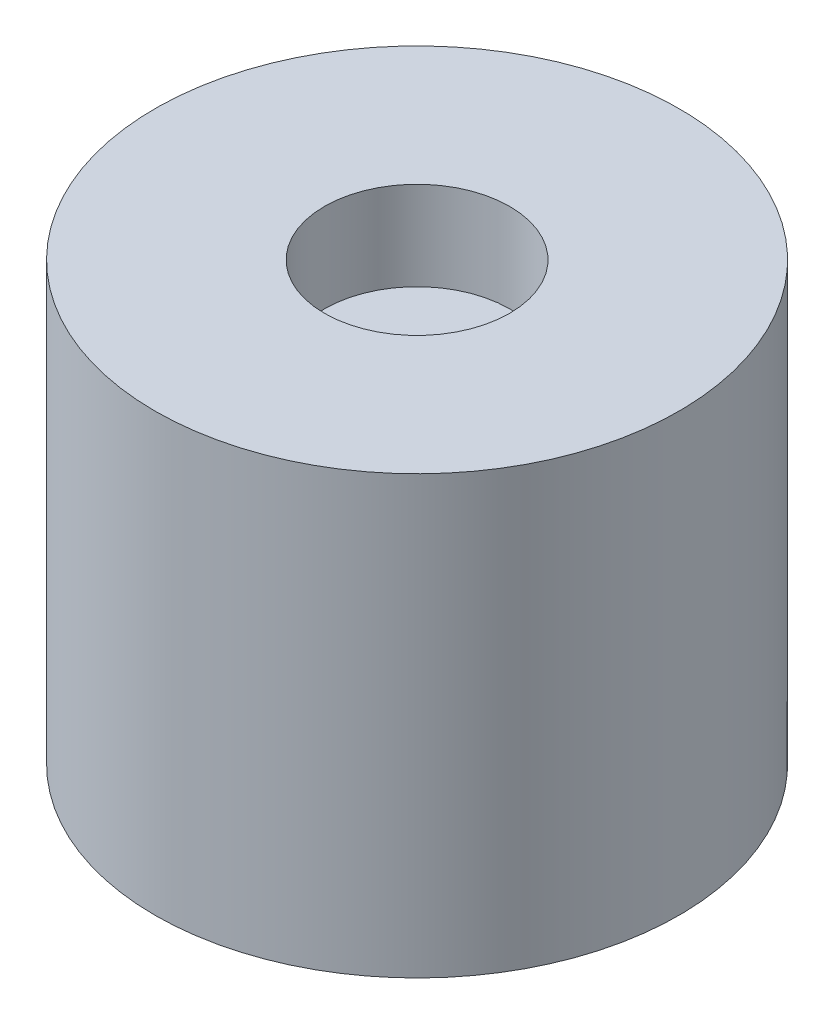
SolidWorks part; units mm, degrees
ref_plane "Front Plane" through (0, 0, 0) normal (0, 0, 1) x (1, 0, 0)
ref_plane "Top Plane" through (0, 0, 0) normal (0, 1, 0) x (1, 0, 0)
ref_plane "Right Plane" through (0, 0, 0) normal (1, 0, 0) x (0, 0, -1)
sketch "Sketch1" plane through (0, 0, 0) normal (0, 1, 0) x (1, 0, 0)
  circle A0 centre (0, 0) radius 6
  dimension "D1" = 12
extrude "Boss-Extrude1" add sketch "Sketch1" along normal blind 10
sketch "Sketch3" plane through (0, 10, 0) normal (0, 1, 0) x (1, 0, 0)
  circle A0 centre (0, 0) radius 2.1209
  dimension "D1" = 4.2418
extrude "Cut-Extrude2" cut sketch "Sketch3" against normal blind 2.032
sketch "Sketch2" plane through (0, 0, 0) normal (0, -1, 0) x (1, 0, 0)
  circle A0 centre (0, 0) radius 4.05
  dimension "D1" = 8.1
extrude "Cut-Extrude1" cut sketch "Sketch2" against normal offset from surface (6.968 mm away) 1
